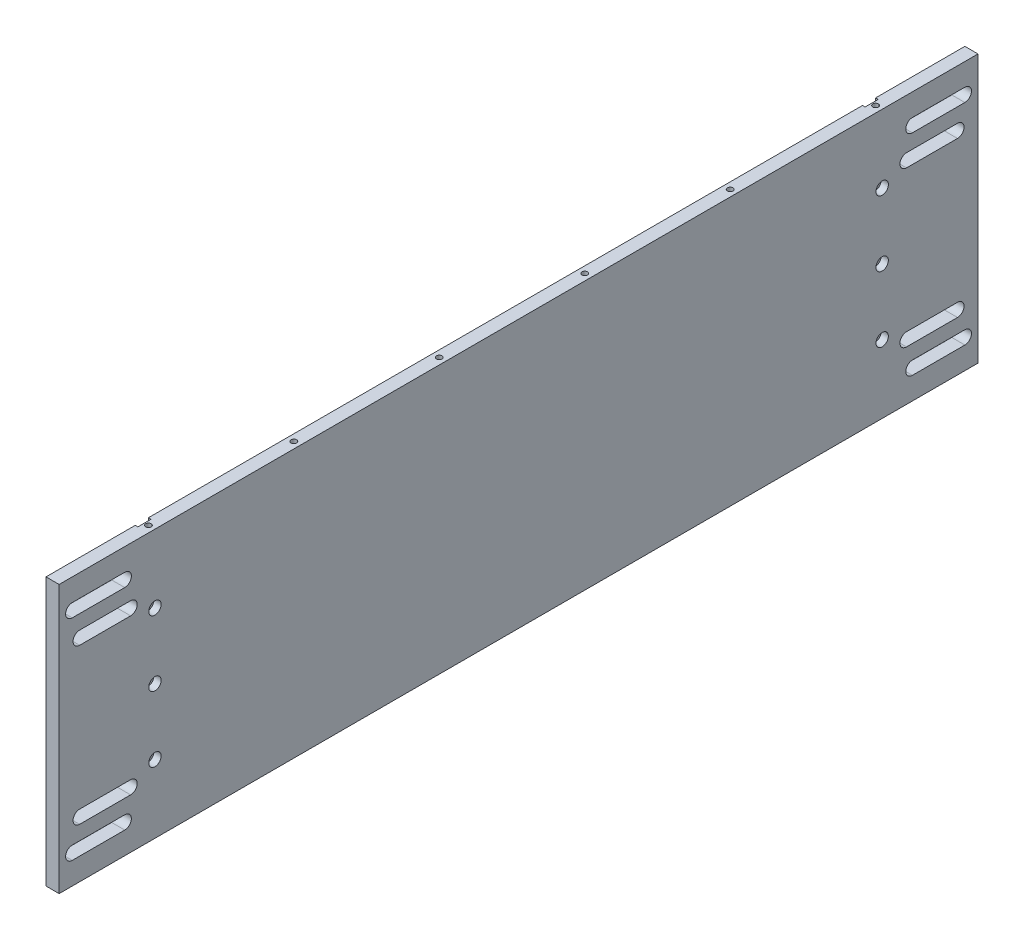
SolidWorks part; units mm, degrees
material "6061 Alloy"
ref_plane "Front Plane" through (0, 0, 0) normal (0, 0, 1) x (1, 0, 0)
ref_plane "Top Plane" through (0, 0, 0) normal (0, 1, 0) x (1, 0, 0)
ref_plane "Right Plane" through (0, 0, 0) normal (1, 0, 0) x (0, 0, -1)
sketch "Sketch1" plane through (0, 0, 0) normal (1, 0, 0) x (0, 0, -1)
  line L1 (0, 0) -> (444.5, 0)
  line L2 (0, 0) -> (0, 129.54)
  line L3 (0, 129.54) -> (444.5, 129.54)
  line L4 (444.5, 0) -> (444.5, 129.54)
  dimension "D1" = 444.5
  dimension "D2" = 129.54
extrude "Boss-Extrude1" add sketch "Sketch1" along normal blind 6.35
hole_wizard "CBORE for #6 Socket Head Cap Screw1" positions "Sketch15" profile "Sketch14" counterbore size "#6" standard "ANSI Inch" end condition through all
sketch "Sketch15" plane through (6.35, 0, 0) normal (1, 0, 0) x (0, 0, -1)
  line L1 (444.5, 129.54) -> (0, 129.54) construction
  line L3 (222.25, 129.54) -> (222.25, 0) construction
  line L4 (0, 0) -> (444.5, 0) construction
  line L6 (46.355, 96.52) -> (46.355, 33.02) construction
  line L8 (398.145, 96.52) -> (398.145, 33.02) construction
  line L9 (444.5, 64.77) -> (0, 64.77) construction
  line L10 (444.5, 0) -> (444.5, 129.54) construction
  line L11 (0, 129.54) -> (0, 0) construction
  point P0 (46.355, 64.77)
  point P8 (398.145, 64.77)
  point P13 (46.355, 96.52)
  point P15 (46.355, 33.02)
  point P17 (398.145, 96.52)
  point P19 (398.145, 33.02)
  dimension "D1" = 175.895
  dimension "D3" = 175.895
  dimension "D4" = 31.75
  dimension "D5" = 31.75
  dimension "D6" = 31.75
  dimension "D7" = 31.75
sketch "Sketch14" plane through (6.35, 64.77, -46.355) normal (0, 1, 0) x (0, 0, -1)
  line L0 (0, 0) -> (0, 6.35)
  line L1 (0, 6.35) -> (1.8288, 6.35)
  line L3 (1.8288, 6.35) -> (1.8288, 3.5052)
  line L4 (1.8288, 3.5052) -> (3, 3.5052)
  line L5 (3, 3.5052) -> (3, 0)
  line L7 (3, 0) -> (0, 0)
  line L11 (0, -6.35) -> (0, 107.95) construction
  dimension "Thru Hole Dia." = 3.6576
  dimension "Thru Hole Depth" = 6.35
  dimension "C'Bore Dia." = 6
  dimension "C'Bore Depth" = 3.5052
sketch "Sketch16" plane through (6.35, 0, 0) normal (1, 0, 0) x (0, 0, -1)
  line L0 (222.25, 129.54) -> (222.25, 0) construction
  line L1 (444.5, 129.54) -> (0, 129.54) construction
  line L2 (0, 0) -> (444.5, 0) construction
  line L3 (6.35, 115.57) -> (31.75, 115.57) construction
  line L4 (0, 129.54) -> (0, 0) construction
  line L5 (0, 64.77) -> (444.5, 64.77) construction
  line L6 (444.5, 0) -> (444.5, 129.54) construction
  line L7 (6.35, 118.7704) -> (31.75, 118.7704)
  line L8 (6.35, 112.3696) -> (31.75, 112.3696)
  line L9 (434.5817, 27.27) -> (409.9183, 27.27) construction
  line L10 (434.5817, 24.095) -> (409.9183, 24.095)
  line L11 (434.5817, 30.445) -> (409.9183, 30.445)
  line L12 (434.5817, 102.27) -> (409.9183, 102.27) construction
  line L13 (434.5817, 105.445) -> (409.9183, 105.445)
  line L14 (434.5817, 99.095) -> (409.9183, 99.095)
  line L15 (6.35, 13.97) -> (31.75, 13.97) construction
  line L16 (6.35, 10.7696) -> (31.75, 10.7696)
  line L17 (6.35, 17.1704) -> (31.75, 17.1704)
  line L18 (438.15, 115.57) -> (412.75, 115.57) construction
  line L19 (438.15, 118.7704) -> (412.75, 118.7704)
  line L20 (438.15, 112.3696) -> (412.75, 112.3696)
  line L21 (9.9183, 102.27) -> (34.5817, 102.27) construction
  line L22 (9.9183, 105.445) -> (34.5817, 105.445)
  line L23 (9.9183, 99.095) -> (34.5817, 99.095)
  line L24 (9.9183, 27.27) -> (34.5817, 27.27) construction
  line L25 (9.9183, 24.095) -> (34.5817, 24.095)
  line L26 (9.9183, 30.445) -> (34.5817, 30.445)
  line L27 (438.15, 13.97) -> (412.75, 13.97) construction
  line L28 (438.15, 10.7696) -> (412.75, 10.7696)
  line L29 (438.15, 17.1704) -> (412.75, 17.1704)
  arc A0 (6.35, 118.7704) -> (6.35, 112.3696) centre (6.35, 115.57) ccw
  arc A1 (31.75, 112.3696) -> (31.75, 118.7704) centre (31.75, 115.57) ccw
  arc A2 (434.5817, 24.095) -> (434.5817, 30.445) centre (434.5817, 27.27) ccw
  arc A3 (409.9183, 30.445) -> (409.9183, 24.095) centre (409.9183, 27.27) ccw
  arc A4 (434.5817, 105.445) -> (434.5817, 99.095) centre (434.5817, 102.27) cw
  arc A5 (409.9183, 99.095) -> (409.9183, 105.445) centre (409.9183, 102.27) cw
  arc A6 (6.35, 10.7696) -> (6.35, 17.1704) centre (6.35, 13.97) cw
  arc A7 (31.75, 17.1704) -> (31.75, 10.7696) centre (31.75, 13.97) cw
  arc A8 (438.15, 118.7704) -> (438.15, 112.3696) centre (438.15, 115.57) cw
  arc A9 (412.75, 112.3696) -> (412.75, 118.7704) centre (412.75, 115.57) cw
  arc A10 (9.9183, 105.445) -> (9.9183, 99.095) centre (9.9183, 102.27) ccw
  arc A11 (34.5817, 99.095) -> (34.5817, 105.445) centre (34.5817, 102.27) ccw
  arc A12 (9.9183, 24.095) -> (9.9183, 30.445) centre (9.9183, 27.27) cw
  arc A13 (34.5817, 30.445) -> (34.5817, 24.095) centre (34.5817, 27.27) cw
  arc A14 (438.15, 10.7696) -> (438.15, 17.1704) centre (438.15, 13.97) ccw
  arc A15 (412.75, 17.1704) -> (412.75, 10.7696) centre (412.75, 13.97) ccw
  point P14 (19.05, 115.57)
  point P20 (422.25, 27.27)
  point P28 (422.25, 102.27)
  point P35 (19.05, 13.97)
  point P42 (425.45, 115.57)
  point P49 (22.25, 102.27)
  point P56 (22.25, 27.27)
  point P63 (425.45, 13.97)
  dimension "D1" = 203.2
  dimension "D2" = 200
  dimension "D3" = 50.8
  dimension "D4" = 37.5
  dimension "D5" = 25.4
  dimension "D6" = 24.6634
extrude "Cut-Extrude1" cut sketch "Sketch16" against normal through all
hole_wizard "Tap Drill for #6-32 Tap1" positions "Sketch17" profile "Sketch18" hole size "#6-32" standard "ANSI Inch"
sketch "Sketch17" plane through (62.7471, 129.54, -312.393) normal (0, 1, 0) x (0, 0, 1)
  point P0 (-85.752, -59.5721)
  point P3 (-15.394, -59.5721)
  point P6 (54.964, -59.5721)
  point P9 (125.322, -59.5721)
  point P12 (195.68, -59.5721)
  point P15 (266.038, -59.5721)
  point P18 (266.038, -129.9301)
  point P21 (266.038, -200.2881)
  point P24 (266.038, -270.6461)
  point P27 (266.038, -341.0041)
  point P30 (266.038, -411.3621)
  point P33 (195.68, -411.3621)
  point P36 (125.322, -411.3621)
  point P39 (54.964, -411.3621)
  point P42 (-15.394, -411.3621)
  point P45 (-85.752, -411.3621)
  point P48 (-85.752, -341.0041)
  point P51 (-85.752, -270.6461)
  point P54 (-85.752, -200.2881)
  point P57 (-85.752, -129.9301)
sketch "Sketch18" plane through (3.175, 129.54, -398.145) normal (1, 0, 0) x (0, 0, 1)
  line L0 (0, 0) -> (0, 18.5927)
  line L1 (0, 18.5927) -> (1.3525, 17.78)
  line L2 (1.3525, 17.78) -> (1.3525, 0)
  line L3 (1.3525, 0) -> (0, 0)
  line L4 (0, 18.5927) -> (-1.3525, 17.78) construction
  line L5 (0, -6.35) -> (0, 107.95) construction
  dimension "Hole Dia." = 2.7051
  dimension "Hole Depth" = 17.78
  dimension "Drill Angle" = 118
hole_wizard "Tap Drill for #6-32 Tap2" positions "Sketch19" profile "Sketch20" hole size "#6-32" standard "ANSI Inch"
sketch "Sketch19" plane through (62.7471, 0, -312.393) normal (0, -1, 0) x (0, 0, -1)
  point P0 (85.752, -411.3621)
  point P3 (15.394, -411.3621)
  point P6 (-54.964, -411.3621)
  point P9 (-125.322, -411.3621)
  point P12 (-195.68, -411.3621)
  point P15 (-266.038, -411.3621)
  point P18 (-266.038, -341.0041)
  point P21 (-266.038, -270.6461)
  point P24 (-266.038, -200.2881)
  point P27 (-266.038, -129.9301)
  point P30 (-266.038, -59.5721)
  point P33 (-195.68, -59.5721)
  point P36 (-125.322, -59.5721)
  point P39 (-54.964, -59.5721)
  point P42 (15.394, -59.5721)
  point P45 (85.752, -59.5721)
  point P48 (85.752, -130.0063)
  point P51 (85.752, -200.3643)
  point P54 (85.752, -270.7223)
  point P57 (85.752, -341.0803)
sketch "Sketch20" plane through (-348.615, 0, -398.145) normal (1, 0, 0) x (0, 0, -1)
  line L0 (0, 0) -> (0, 18.5927)
  line L1 (0, 18.5927) -> (1.3525, 17.78)
  line L2 (1.3525, 17.78) -> (1.3525, 0)
  line L3 (1.3525, 0) -> (0, 0)
  line L4 (0, 18.5927) -> (-1.3525, 17.78) construction
  line L5 (0, -6.35) -> (0, 107.95) construction
  dimension "Hole Dia." = 2.7051
  dimension "Hole Depth" = 17.78
  dimension "Drill Angle" = 118
sketch "Sketch21" plane through (0, 0, 0) normal (-1, 0, 0) x (0, 0, 1)
  line L0 (-444.5, 129.54) -> (0, 129.54) construction
  line L1 (-401.32, 0) -> (-394.97, 0)
  line L2 (-401.32, 0) -> (-401.32, 129.54)
  line L3 (-401.32, 129.54) -> (-394.97, 129.54)
  line L4 (-394.97, 0) -> (-394.97, 129.54)
  line L5 (-401.32, 0) -> (-394.97, 129.54) construction
  line L6 (-401.32, 129.54) -> (-394.97, 0) construction
  line L8 (-43.18, 0) -> (-49.53, 0)
  line L9 (-43.18, 0) -> (-43.18, 129.54)
  line L10 (-43.18, 129.54) -> (-49.53, 129.54)
  line L11 (-49.53, 0) -> (-49.53, 129.54)
  line L12 (-43.18, 0) -> (-49.53, 129.54) construction
  line L13 (-43.18, 129.54) -> (-49.53, 0) construction
  point P0 (-398.145, 64.77)
  point P8 (-46.355, 64.77)
  dimension "D1" = 6.35
  dimension "D2" = 6.35
extrude "Cut-Extrude2" cut sketch "Sketch21" against normal blind 1.27
